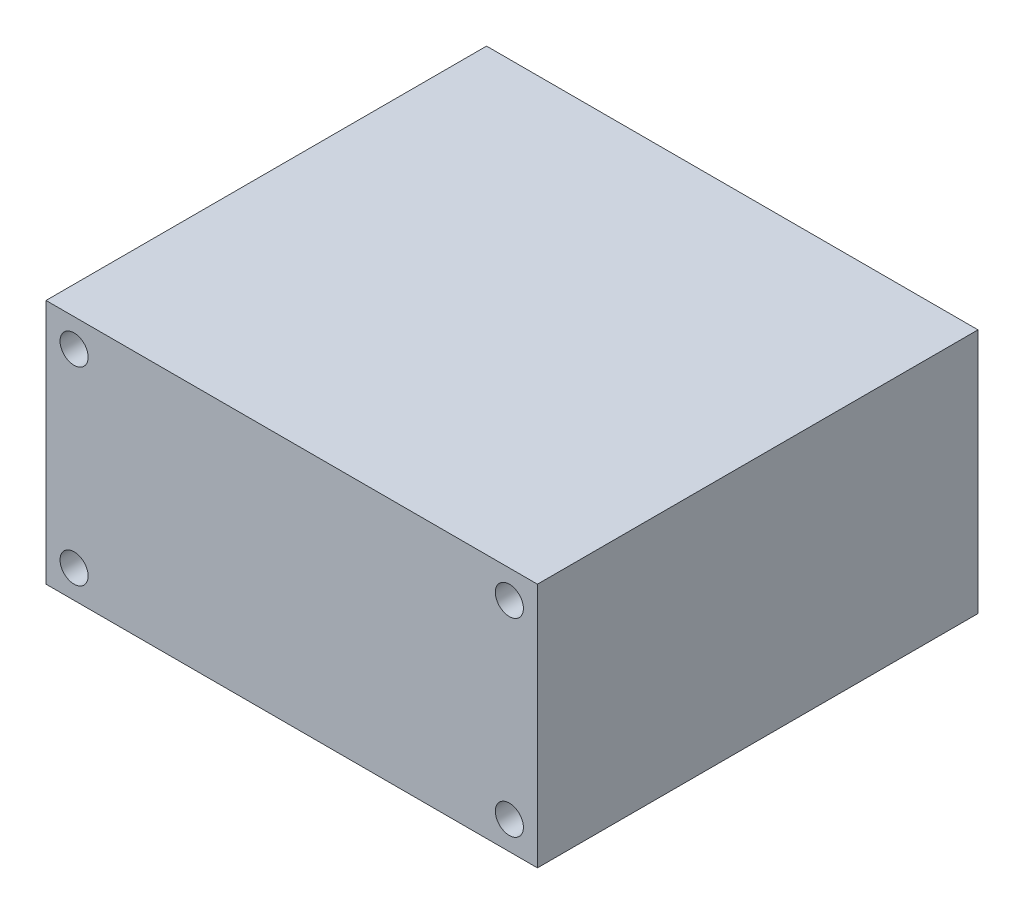
SolidWorks part; units mm, degrees
ref_plane "前视基准面" through (0, 0, 0) normal (0, 0, 1) x (1, 0, 0)
ref_plane "上视基准面" through (0, 0, 0) normal (0, 1, 0) x (1, 0, 0)
ref_plane "右视基准面" through (0, 0, 0) normal (1, 0, 0) x (0, 0, -1)
other "Configuration Table"
sketch "草图2" plane through (0, 0, 0) normal (0, 0, 1) x (1, 0, 0)
  line L1 (-56, 28) -> (0, 28)
  line L2 (-56, 28) -> (-56, 0)
  line L3 (-56, 0) -> (0, 0)
  line L4 (0, 28) -> (0, 0)
  line L5 (-56, 28) -> (0, 0) construction
  line L6 (-56, 0) -> (0, 28) construction
  point P0 (-28, 14)
  dimension "D1" = 56
  dimension "D2" = 28
extrude "凸台-拉伸1" add sketch "草图2" along normal blind 50.2
sketch "草图4" plane through (0, 0, 50.2) normal (0, 0, 1) x (1, 0, 0)
  line L0 (0, 0) -> (0, 28) construction
  line L1 (-52.8, 3.2) -> (-3.2, 3.2) construction
  line L2 (-52.8, 3.2) -> (-52.8, 24.8) construction
  line L3 (-52.8, 24.8) -> (-3.2, 24.8) construction
  line L4 (-3.2, 3.2) -> (-3.2, 24.8) construction
  line L5 (-52.8, 3.2) -> (-3.2, 24.8) construction
  line L6 (-52.8, 24.8) -> (-3.2, 3.2) construction
  line L7 (-28, 0) -> (-28, 14) construction
  line L8 (-56, 0) -> (0, 0) construction
  circle A0 centre (-52.8, 24.8) radius 1.6
  circle A1 centre (-3.2, 3.2) radius 1.6
  circle A2 centre (-52.8, 3.2) radius 1.6
  circle A3 centre (-3.2, 24.8) radius 1.6
  point P0 (-28, 14)
  point P8 (0, 14)
  point P16 (0, 0)
  dimension "D3" = 3.2
  dimension "D4" = 3.2
  dimension "D5" = 3.2
  dimension "D6" = 3.2
  dimension "D1" = 21.6
  dimension "D2" = 49.6
extrude "切除-拉伸1" cut sketch "草图4" against normal blind 50.2 contours A0 | A2 | A1 | A3
